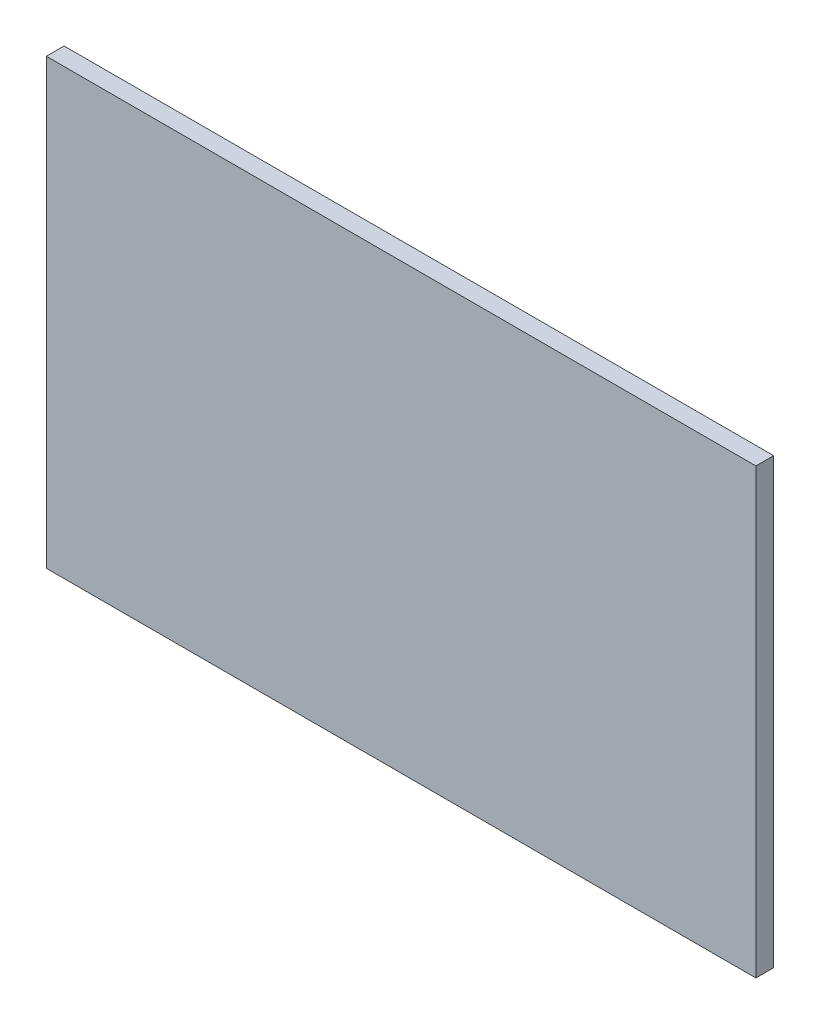
SolidWorks part; units mm, degrees
material "Oak"
ref_plane "Front Plane" through (0, 0, 0) normal (0, 0, 1) x (1, 0, 0)
ref_plane "Top Plane" through (0, 0, 0) normal (0, 1, 0) x (1, 0, 0)
ref_plane "Right Plane" through (0, 0, 0) normal (1, 0, 0) x (0, 0, -1)
sketch "Sketch1" plane through (0, 0, 0) normal (0, 0, 1) x (1, 0, 0)
  line L1 (0, 0) -> (400, 0)
  line L2 (0, 0) -> (0, 250)
  line L3 (0, 250) -> (400, 250)
  line L4 (400, 0) -> (400, 250)
extrude "Boss-Extrude1" add sketch "Sketch1" along normal blind 10
